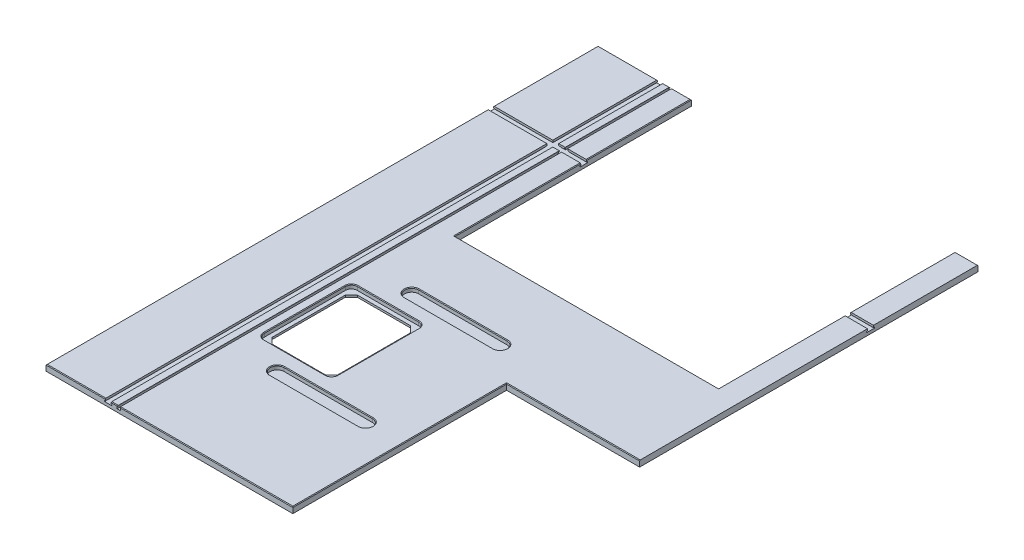
SolidWorks part; units mm, degrees
material "Oak"
ref_plane "Front Plane" through (0, 0, 0) normal (0, 0, 1) x (1, 0, 0)
ref_plane "Top Plane" through (0, 0, 0) normal (0, 1, 0) x (1, 0, 0)
ref_plane "Right Plane" through (0, 0, 0) normal (1, 0, 0) x (0, 0, -1)
sketch "Sketch1" plane through (0, 0, 0) normal (0, 1, 0) x (1, 0, 0)
  line L4 (1219.2, 0) -> (1219.2, 1771.65)
  line L5 (1219.2, 1771.65) -> (0, 1771.65)
  line L7 (0, 0) -> (1219.2, 0)
  line L8 (0, 1771.65) -> (0, 0)
  dimension "D1" = 1219.2
  dimension "D5" = 1771.65
extrude "Boss-Extrude1" add sketch "Sketch1" against normal blind 19.05
sketch "Sketch3" plane through (0, 0, 0) normal (0, 1, 0) x (1, 0, 0)
  line L0 (0, 0) -> (1219.2, 0) construction
  line L1 (792.1625, 685.8) -> (1300.1625, 685.8)
  line L2 (792.1625, 685.8) -> (792.1625, 0)
  line L3 (792.1625, 0) -> (1300.1625, 0)
  line L4 (1300.1625, 685.8) -> (1300.1625, 0)
  dimension "D1" = 508
  dimension "D2" = 792.1625
  dimension "D3" = 685.8
extrude "Cut-Extrude2" cut sketch "Sketch3" against normal through all
sketch "Sketch5" plane through (0, 0, 0) normal (0, 1, 0) x (1, 0, 0)
  line L1 (299.1104, 1771.65) -> (1145.54, 1771.65)
  line L2 (299.1104, 1771.65) -> (299.1104, 1012.825)
  line L3 (299.1104, 1012.825) -> (1145.54, 1012.825)
  line L4 (1145.54, 1771.65) -> (1145.54, 1012.825)
  line L7 (1219.2, 1771.65) -> (0, 1771.65) construction
  dimension "D1" = 299.1104
  dimension "D2" = 846.4296
  dimension "D3" = 1012.825
extrude "Cut-Extrude4" cut sketch "Sketch5" against normal through all
sketch "Sketch18" plane through (299.1104, 0, 0) normal (1, 0, 0) x (0, 0, -1)
  line L4 (685.8, 0) -> (685.8, -19.05)
  line L5 (685.8, -19.05) -> (1771.65, -19.05)
  line L6 (1771.65, -19.05) -> (1771.65, 0)
  line L7 (1771.65, 0) -> (685.8, 0)
  line L9 (1009.6018, -19.05) -> (1771.65, -19.05)
  line L10 (1771.65, -19.05) -> (1771.65, 0)
  line L11 (1771.65, 0) -> (1014.8275, 0)
  arc A1 (1014.8275, 0) -> (1009.6018, -19.05) centre (1430.274, -124.206) ccw
  point P3 (1021.5483, 20.5912)
  dimension "D3" = 433.6161
  dimension "D1" = 1430.274
  dimension "D2" = 124.206
  dimension "D4" = 0
extrude "Cut-Extrude12" cut sketch "Sketch18" along normal up to surface (846.4296 mm away) up to face at (1145.54, -9.525, -1392.2375)
sketch "Sketch7" plane through (0, 0, 0) normal (0, 1, 0) x (1, 0, 0)
  line L1 (281.3685, 717.55) -> (478.2185, 717.55)
  line L2 (262.3185, 698.5) -> (262.3185, 438.15)
  line L3 (281.3685, 419.1) -> (478.2185, 419.1)
  line L4 (497.2685, 698.5) -> (497.2685, 438.15)
  arc A0 (497.2685, 438.15) -> (478.2185, 419.1) centre (478.2185, 438.15) cw
  arc A1 (281.3685, 419.1) -> (262.3185, 438.15) centre (281.3685, 438.15) cw
  arc A2 (262.3185, 698.5) -> (281.3685, 717.55) centre (281.3685, 698.5) cw
  arc A3 (478.2185, 717.55) -> (497.2685, 698.5) centre (478.2185, 698.5) cw
  dimension "D5" = 19.05
  dimension "D1" = 262.3185
  dimension "D2" = 234.95
  dimension "D3" = 419.1
  dimension "D4" = 298.45
extrude "Cut-Extrude5" cut sketch "Sketch7" against normal blind 12.7
sketch "Sketch8" plane through (0, -12.7, 0) normal (0, 1, 0) x (1, 0, 0)
  line L0 (294.0685, 704.85) -> (275.0185, 685.8)
  line L1 (294.0685, 704.85) -> (465.5185, 704.85)
  line L2 (275.0185, 685.8) -> (275.0185, 450.85)
  line L3 (294.0685, 431.8) -> (465.5185, 431.8)
  line L4 (484.5685, 685.8) -> (484.5685, 450.85)
  line L5 (379.7935, 369.414) -> (379.7935, 778.191) construction
  line L6 (219.5895, 568.325) -> (559.0988, 568.325) construction
  line L7 (465.5185, 704.85) -> (484.5685, 685.8)
  line L8 (465.5185, 431.8) -> (484.5685, 450.85)
  line L9 (294.0685, 431.8) -> (275.0185, 450.85)
  point P4 (379.7935, 704.85)
  dimension "D5" = 19.05
  dimension "D1" = 275.0185
  dimension "D2" = 209.55
  dimension "D3" = 431.8
  dimension "D4" = 273.05
  dimension "D6" = 19.05
extrude "Cut-Extrude6" cut sketch "Sketch8" against normal through all
sketch "Sketch17" plane through (0, 0, 0) normal (0, 1, 0) x (1, 0, 0)
  line L0 (389.4129, 784.225) -> (673.1309, 784.225) construction
  line L1 (389.4129, 806.45) -> (673.1309, 806.45)
  line L2 (389.4129, 762) -> (673.1309, 762)
  line L5 (389.4129, 352.425) -> (673.1309, 352.425) construction
  line L6 (389.4129, 330.2) -> (673.1309, 330.2)
  line L7 (389.4129, 374.65) -> (673.1309, 374.65)
  arc A0 (389.4129, 806.45) -> (389.4129, 762) centre (389.4129, 784.225) ccw
  arc A1 (673.1309, 762) -> (673.1309, 806.45) centre (673.1309, 784.225) ccw
  arc A2 (389.4129, 330.2) -> (389.4129, 374.65) centre (389.4129, 352.425) cw
  arc A3 (673.1309, 374.65) -> (673.1309, 330.2) centre (673.1309, 352.425) cw
  point P2 (531.2719, 784.225)
  point P13 (531.2719, 352.425)
  dimension "D5" = 22.225
  dimension "D1" = 431.8
  dimension "D2" = 352.425
  dimension "D3" = 389.4129
  dimension "D4" = 283.718
extrude "Cut-Extrude11" cut sketch "Sketch17" against normal blind 12.7
sketch "Sketch12" plane through (0, 0, 0) normal (0, 0, 1) x (1, 0, 0)
  line L32 (0, 0) -> (792.1625, 0) construction
  line L33 (190.2079, 0) -> (209.2579, 0)
  line L36 (262.3185, -12.7) -> (262.3185, 0) construction
  line L37 (230.0859, 0) -> (237.4519, 0)
  line L40 (120.6953, 34.7588) -> (120.6953, -55.09) construction
  line L41 (199.7329, 11.4165) -> (199.7329, 27.3169) construction
  line L42 (233.7689, -9.525) -> (233.7689, 29.7944) construction
  line L47 (190.2079, -6.096) -> (187.7949, -6.096)
  line L48 (190.2079, 0) -> (190.2079, -6.096)
  line L49 (237.4519, -2.54) -> (237.4519, 0)
  line L50 (239.4839, -2.54) -> (237.4519, -2.54)
  line L51 (239.4839, -9.525) -> (239.4839, -2.54)
  line L52 (228.0539, -9.525) -> (239.4839, -9.525)
  line L53 (228.0539, -2.54) -> (228.0539, -9.525)
  line L54 (230.0859, -2.54) -> (228.0539, -2.54)
  line L55 (230.0859, 0) -> (230.0859, -2.54)
  line L56 (209.2579, -6.096) -> (209.2579, 0)
  line L57 (211.6709, -6.096) -> (209.2579, -6.096)
  line L58 (211.6709, -9.525) -> (211.6709, -6.096)
  line L59 (187.7949, -9.525) -> (211.6709, -9.525)
  line L60 (187.7949, -6.096) -> (187.7949, -9.525)
  point P7 (189.0014, -6.096)
  line M43 (792.1625, 0) -> (0, 0)
  dimension "D2" = 34.036
  dimension "D3" = 2.54
  dimension "D4" = 9.525
  dimension "D5" = 11.43
  dimension "D6" = 7.366
  dimension "D7" = 6.096
  dimension "D9" = 23.876
  dimension "D10" = 19.05
  dimension "D11" = 32.2326
extrude "Cut-Extrude8" cut sketch "Sketch12" against normal through all contours L47 L60 L59 L58 L57 L56 L48 M43 | L55 L54 L53 L52 L51 L50 L49 M43
sketch "Sketch16" plane through (0, 0, 0) normal (-1, 0, 0) x (0, 0, 1)
  line L0 (-1771.65, 0) -> (0, 0) construction
  line L1 (-1438.8084, -9.525) -> (-1414.4244, -9.525)
  line L2 (-1438.8084, -9.525) -> (-1438.8084, -5.969)
  line L3 (-1438.8084, -5.969) -> (-1436.1414, -5.969)
  line L4 (-1414.4244, -9.525) -> (-1414.4244, -5.969)
  line L5 (-1436.1414, 0) -> (-1417.0914, 0)
  line L6 (-1436.1414, 0) -> (-1436.1414, -5.969)
  line L8 (-1417.0914, 0) -> (-1417.0914, -5.969)
  line L9 (-1426.6164, -26.666) -> (-1426.6164, 16.3649) construction
  line L10 (-1417.0914, -5.969) -> (-1414.4244, -5.969)
  line L12 (-1012.825, -6.9062) -> (-1012.825, 0) construction
  dimension "D1" = 404.2664
  dimension "D2" = 24.384
  dimension "D3" = 19.05
  dimension "D4" = 5.969
  dimension "D5" = 9.525
extrude "Cut-Extrude10" cut sketch "Sketch16" against normal through all
chamfer "Chamfer2" distance 2.032 angle 45 32 edges at (299.1104, 0, -1214.9582) (722.3252, 0, -1012.825) (1145.54, 0, -1214.9582) (1145.54, 0, -1603.8957) (1182.37, 0, -1771.65) (299.1104, 0, -1603.8957) (268.2811, 0, -1771.65) (219.6719, 0, -1771.65) (95.1039, 0, -1771.65) (0, 0, -1603.8957) (1005.6812, 0, -685.8) (792.1625, 0, -342.9) (514.8072, 0, 0) (219.6719, 0, 0) (0, 0, -708.5457) (95.1039, 0, 0) (267.8981, 0, -424.6796) (262.3185, 0, -568.325) (267.8981, 0, -711.9704) (379.7935, 0, -717.55) (491.6889, 0, -711.9704) (497.2685, 0, -568.325) (491.6889, 0, -424.6796) (379.7935, 0, -419.1) (531.2719, 0, -330.2) (367.1879, 0, -352.425) (531.2719, 0, -374.65) (695.3559, 0, -352.425) (695.3559, 0, -784.225) (531.2719, 0, -806.45) (367.1879, 0, -784.225) (531.2719, 0, -762)
